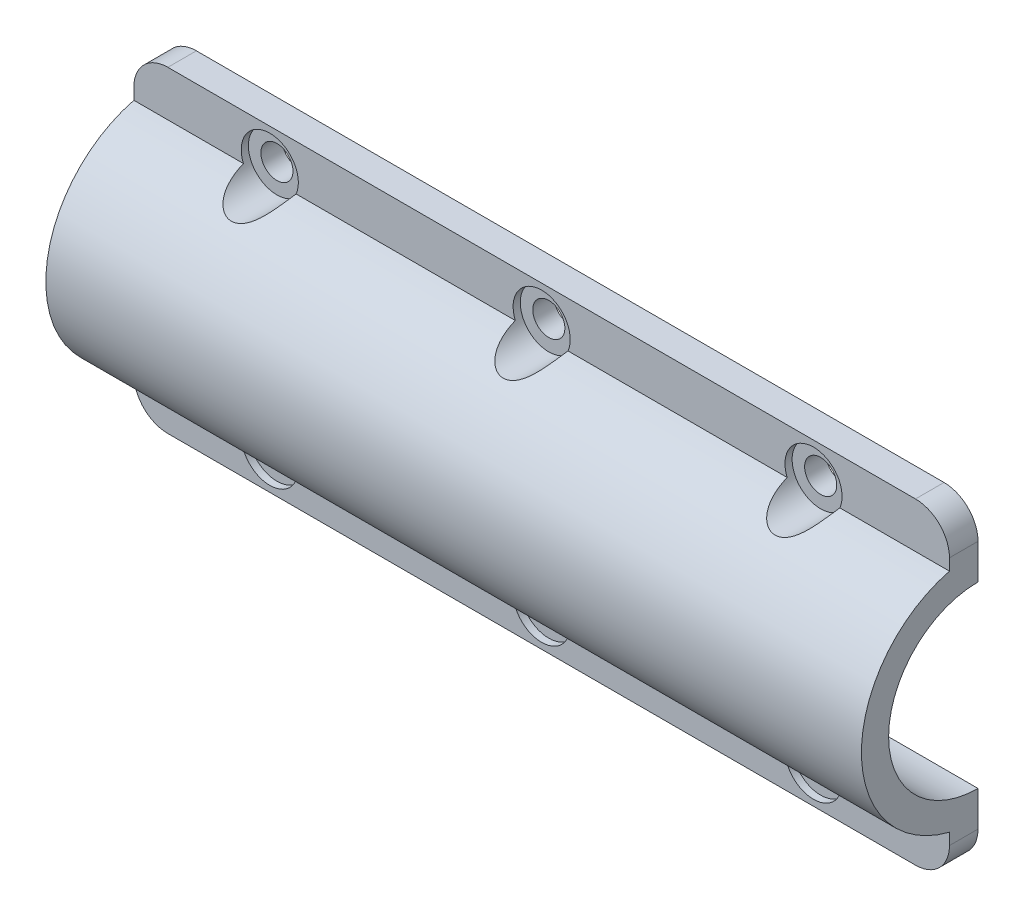
SolidWorks part; units mm, degrees
material "ABS"
ref_plane "X-Y Datum" through (0, 0, 0) normal (0, 0, 1) x (1, 0, 0)
ref_plane "X-Z Datum" through (0, 0, 0) normal (0, 1, 0) x (1, 0, 0)
ref_plane "Y-Z Datum" through (0, 0, 0) normal (1, 0, 0) x (0, 0, -1)
sketch "Sketch1" plane through (0, 0, 0) normal (1, 0, 0) x (0, 0, -1)
  line L0 (0, 22.225) -> (0, 17.4625) construction
  line L1 (-4, 22.225) -> (-4, 15.8396)
  line L2 (0, -22.225) -> (-4, -22.225)
  line L3 (-4, 11.8711) -> (-4, 11.3422)
  line L4 (-4, -15.8396) -> (-4, -22.225)
  line L7 (23.8125, 12.065) -> (17.8125, 12.065)
  line L8 (23.8125, -17.4625) -> (23.8125, 12.065)
  line L9 (17.8125, 17.4625) -> (0, 17.4625)
  line L10 (0, -12.5269) -> (0, -17.4625)
  line L11 (0, 17.4625) -> (0, 12.5269)
  line L12 (17.8125, 17.4625) -> (0, 17.4625)
  line L13 (17.8125, 12.065) -> (17.8125, 17.4625)
  line L14 (23.8125, 12.065) -> (17.8125, 12.065)
  line L15 (23.8125, -17.4625) -> (23.8125, 12.065)
  line L17 (0, -12.5269) -> (0, -17.4625)
  line L18 (0, 17.4625) -> (0, 12.5269)
  line L20 (17.8125, 12.065) -> (17.8125, 17.4625)
  line L27 (17.8125, 22.225) -> (0, 22.225) construction
  line L28 (17.8125, 22.225) -> (-4, 22.225)
  line L29 (0, 22.225) -> (0, 17.4625)
  line L31 (0, -22.225) -> (23.8125, -22.225) construction
  line L32 (0, -22.225) -> (23.8125, -22.225)
  line L33 (0, -17.4625) -> (23.8125, -17.4625)
  line L34 (0, -17.4625) -> (23.8125, -17.4625)
  line L35 (0, -17.4625) -> (0, -22.225) construction
  line L36 (0, -17.4625) -> (0, -22.225)
  circle A0 centre (0, 0) radius 12.5269
  arc A1 (0, -12.5269) -> (0, 12.5269) centre (0, 0) ccw
  arc A2 (0, -12.5269) -> (0, 12.5269) centre (0, 0) ccw
  circle A3 centre (0, 0) radius 12.0269
  circle A4 centre (0, 0) radius 12.0269
  circle A5 centre (0, 0) radius 16.3369
  dimension "D5" = 4
  dimension "D1" = 0
  dimension "D2" = 0
  dimension "D3" = 0.5
  dimension "D4" = 3.81
extrude "Boss-Extrude1" add sketch "Sketch1" along normal blind 114.3
sketch "Sketch2" plane through (0, 0, 4) normal (0, 0, 1) x (1, 0, 0)
  circle A0 centre (19.05, -17.376) radius 4
  circle A1 centre (57.15, -17.376) radius 4
  circle A2 centre (95.25, -17.376) radius 4
  point P0 (19.05, -17.376)
  point P1 (57.15, -17.376)
  point P3 (95.25, -17.376)
  dimension "D1" = 8
extrude "Cut-Extrude1" cut sketch "Sketch2" against normal blind 1 and the other way blind 6.35
hole_wizard "M4 Clearance Hole1" positions "Sketch7" profile "Sketch6" hole size "M4" standard "ANSI Metric" end condition through all
sketch "Sketch7" plane through (0, 0, 4) normal (0, 0, 1) x (1, 0, 0)
  point P0 (19.05, -17.376)
  point P3 (57.15, -17.376)
  point P6 (95.25, -17.376)
sketch "Sketch6" plane through (19.05, -17.376, 4) normal (1, 0, 0) x (0, -1, 0)
  line L0 (0, 0) -> (0, 4)
  line L1 (0, 4) -> (2.25, 4)
  line L2 (2.25, 4) -> (2.25, 0)
  line L5 (2.25, 0) -> (0, 0)
  line L11 (0, -6.35) -> (0, 107.95) construction
  dimension "Thru Hole Dia." = 4.5
  dimension "Thru Hole Depth" = 4
mirror "Mirror1" about plane through (0, 0, 0) normal (0, 1, 0) of "M4 Clearance Hole1", "Cut-Extrude1"
fillet "Fillet1" radius 4.7625 4 edges at (114.3, 22.225, 2) (114.3, -22.225, 2) (0, 22.225, 2) (0, -22.225, 2)
